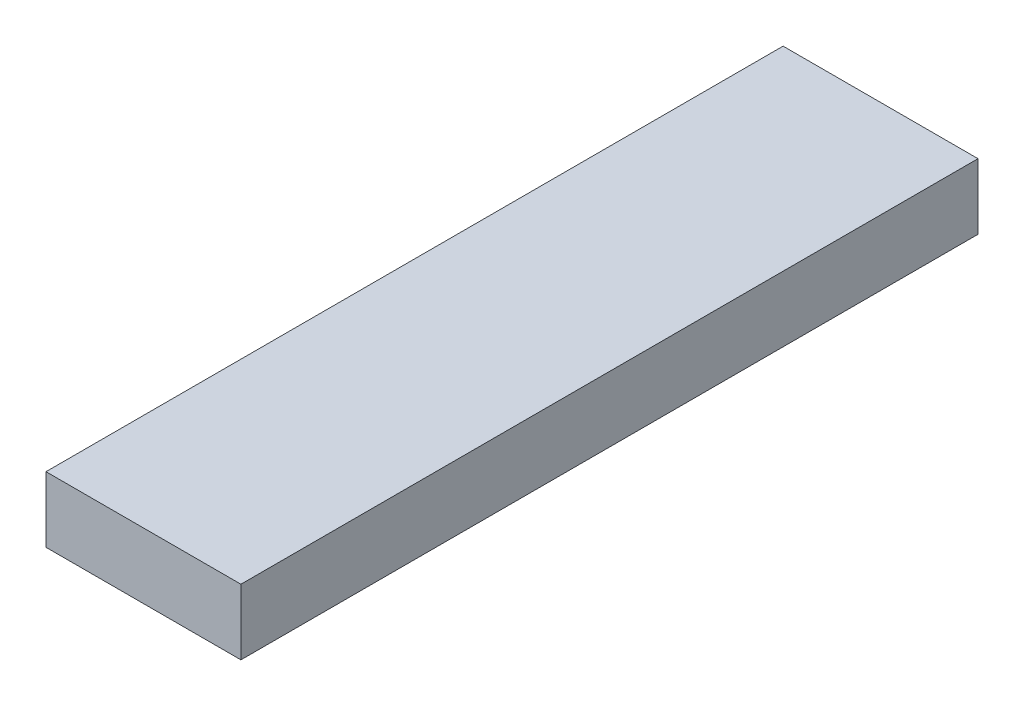
SolidWorks part; units mm, degrees
ref_plane "Front Plane" through (0, 0, 0) normal (0, 0, 1) x (1, 0, 0)
ref_plane "Top Plane" through (0, 0, 0) normal (0, 1, 0) x (1, 0, 0)
ref_plane "Right Plane" through (0, 0, 0) normal (1, 0, 0) x (0, 0, -1)
sketch "Sketch1" plane through (0, 0, 0) normal (0, 1, 0) x (1, 0, 0)
  line L1 (5.95, 22.5) -> (-5.95, 22.5)
  line L2 (5.95, 22.5) -> (5.95, -22.5)
  line L3 (5.95, -22.5) -> (-5.95, -22.5)
  line L4 (-5.95, 22.5) -> (-5.95, -22.5)
  line L5 (5.95, 22.5) -> (-5.95, -22.5) construction
  line L6 (5.95, -22.5) -> (-5.95, 22.5) construction
  point P0 (0, 0)
  dimension "D1" = 11.9
  dimension "D2" = 45
extrude "Boss-Extrude1" add sketch "Sketch1" along normal blind 4
